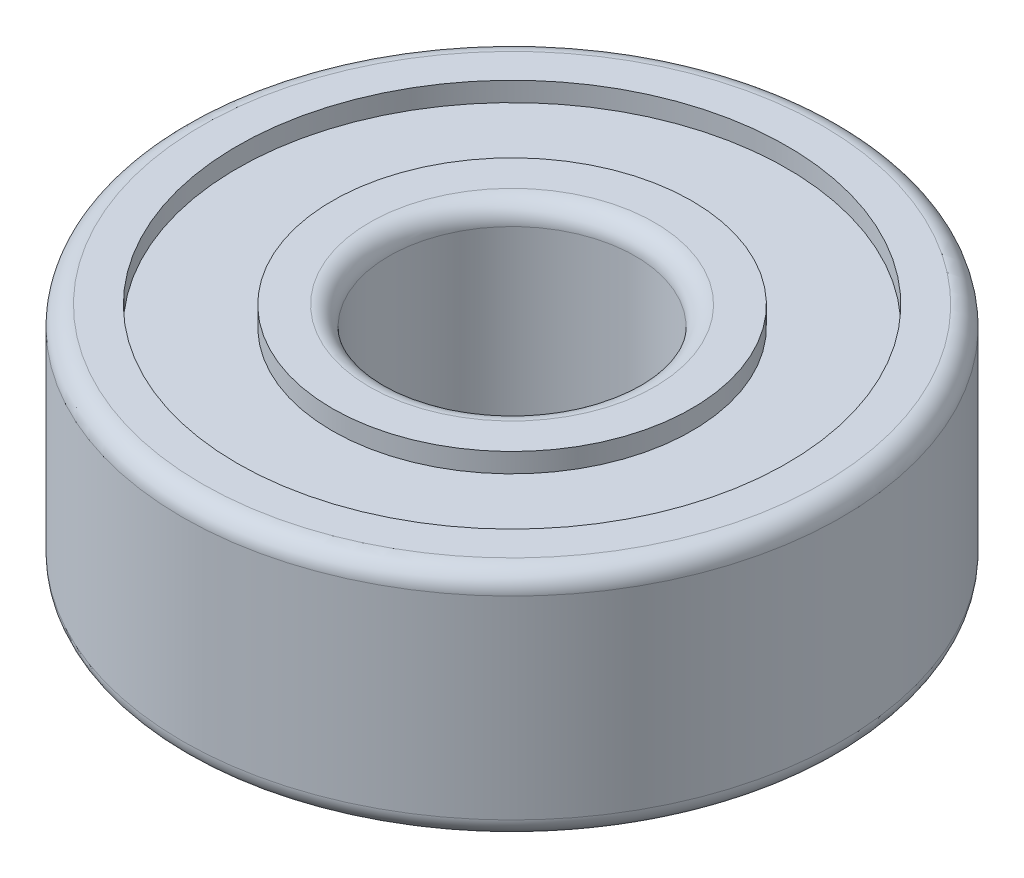
SolidWorks part; units mm, degrees
ref_plane "Front" through (0, 0, 0) normal (0, 0, 1) x (1, 0, 0)
ref_plane "Top" through (0, 0, 0) normal (0, 1, 0) x (1, 0, 0)
ref_plane "Right" through (0, 0, 0) normal (1, 0, 0) x (0, 0, -1)
sketch "Sketch1" plane through (0, 0, 0) normal (0, 1, 0) x (1, 0, 0)
  circle A0 centre (0, 0) radius 6.35
  circle A1 centre (0, 0) radius 17
  dimension "D1" = 12.7
  dimension "D2" = 34
extrude "Boss-Extrude1" add sketch "Sketch1" along normal blind 12
fillet "Fillet1" radius 1 4 edges at (0, 0, 6.35) (0, 12, 6.35) (0, 0, 17) (0, 12, 17)
sketch "Sketch2" plane through (0, 12, 0) normal (0, 1, 0) x (1, 0, 0)
  circle A0 centre (0, 0) radius 14.1791
  circle A1 centre (0, 0) radius 9.2765
extrude "Cut-Extrude1" cut sketch "Sketch2" against normal blind 1
sketch "Sketch3" plane through (0, 0, 0) normal (0, -1, 0) x (1, 0, 0)
  circle A1 centre (0, 0) radius 14.472
  circle A3 centre (0, 0) radius 9.2621
extrude "Cut-Extrude2" cut sketch "Sketch3" against normal blind 1
